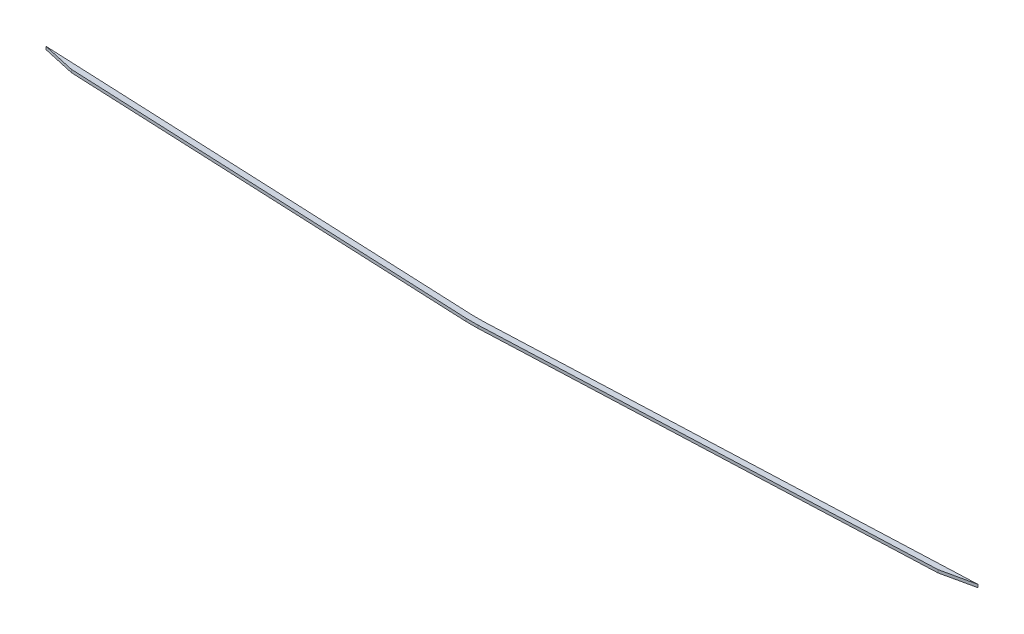
SolidWorks part; units mm, degrees
material "Beech"
ref_plane "Front" through (0, 0, 0) normal (0, 0, 1) x (1, 0, 0)
ref_plane "Top" through (0, 0, 0) normal (0, 1, 0) x (1, 0, 0)
ref_plane "Right" through (0, 0, 0) normal (1, 0, 0) x (0, 0, -1)
sketch "Sketch1" plane through (0, 0, 0) normal (0, 1, 0) x (1, 0, 0)
  line L0 (-6, 6) -> (-465, 26.2203)
  line L1 (-6, 6) -> (6, 6)
  line L2 (-6, 6) -> (-6, 0) construction
  line L3 (6, 0) -> (-6, 0)
  line L4 (6, 6) -> (6, 0) construction
  line L5 (6, 6) -> (495, 26.2066)
  line L6 (495, 26.2066) -> (461.2778, 18.8131)
  line L7 (461.2778, 18.8131) -> (6, 0)
  line L8 (-465, 26.2203) -> (-431.302, 18.7358)
  line L9 (-431.302, 18.7358) -> (-6, 0)
  line L10 (461.2778, 18.8131) -> (490, 20) construction
  line L11 (490, 20) -> (490, 26) construction
  line L12 (-431.302, 18.7358) -> (-460, 20) construction
  line L13 (-460, 20) -> (-460, 26) construction
  dimension "D1" = 12
  dimension "D2" = 6
  dimension "D3" = 460
  dimension "D4" = 5
  dimension "D5" = 10
  dimension "D6" = 10
  dimension "D7" = 5
  dimension "D8" = 490
  dimension "D9" = 20
extrude "Extrude1" add sketch "Sketch1" along normal mid plane 3
